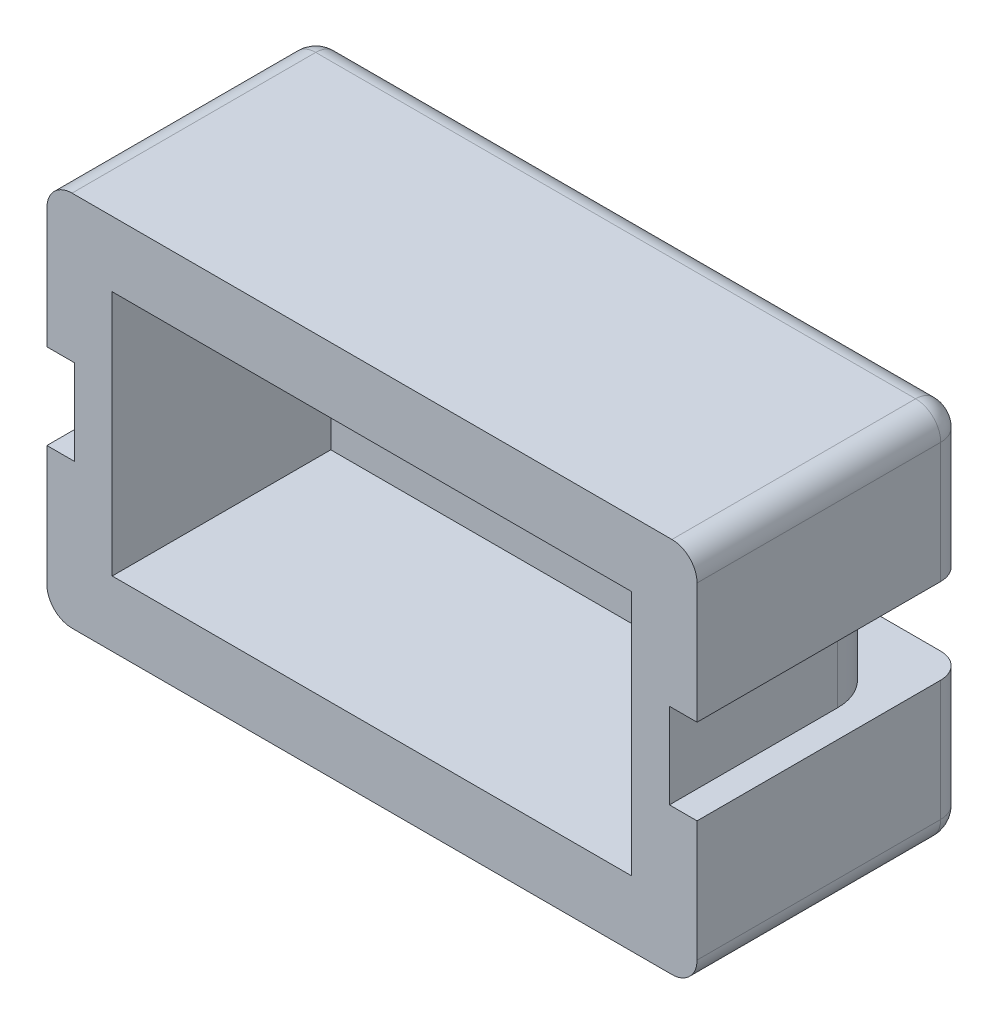
SolidWorks part; units mm, degrees
ref_plane "Front Plane" through (0, 0, 0) normal (0, 0, 1) x (1, 0, 0)
ref_plane "Top Plane" through (0, 0, 0) normal (0, 1, 0) x (1, 0, 0)
ref_plane "Right Plane" through (0, 0, 0) normal (1, 0, 0) x (0, 0, -1)
sketch "Sketch1" plane through (0, 0, 0) normal (0, 0, 1) x (1, 0, 0)
  line L0 (0, -2.7579) -> (0, 2.1887) construction
  line L9 (-3.3744, -0.8) -> (5.2209, -0.8) construction
  line L13 (-2.47, -1.6) -> (2.47, -1.6) construction
  line L14 (2.47, 0) -> (-2.47, 0) construction
  line L15 (-5.97, 0) -> (-5.97, -1.6) construction
  line L16 (6.47, -4.55) -> (-6.47, -4.55)
  line L17 (6.47, -4.55) -> (6.47, 2.95)
  line L18 (6.47, 2.95) -> (-6.47, 2.95)
  line L19 (-6.47, -4.55) -> (-6.47, 2.95)
  line L20 (6.47, -4.55) -> (-6.47, 2.95) construction
  line L21 (6.47, 2.95) -> (-6.47, -4.55) construction
  point P5 (0.9233, -0.8)
  point P12 (0, -0.8)
  dimension "D1" = 0.5
  dimension "D2" = 7.5
extrude "Boss-Extrude1" add sketch "Sketch1" against normal blind 5.35
fillet "Fillet1" radius 0.5 4 edges at (6.47, 2.95, -2.675) (-6.47, 2.95, -2.675) (-6.47, -4.55, -2.675) (6.47, -4.55, -2.675)
sketch "Sketch2" plane through (0, 0, 0) normal (0, 0, 1) x (1, 0, 0)
  line L8 (-5.17, 1.65) -> (-5.17, -3.25)
  line L9 (-5.17, -3.25) -> (5.17, -3.25)
  line L10 (5.17, -3.25) -> (5.17, 1.65)
  line L11 (5.17, 1.65) -> (-5.17, 1.65)
  line L12 (-5.17, 1.65) -> (-5.17, -3.25)
  line L13 (-5.17, -3.25) -> (5.17, -3.25)
  line L14 (5.17, -3.25) -> (5.17, 1.65)
  line L15 (5.17, 1.65) -> (-5.17, 1.65)
  dimension "D1" = 1.3
extrude "Cut-Extrude1" cut sketch "Sketch2" against normal offset from surface (4.35 mm away) 1 up to face at (0, -0.8, -5.35)
sketch "Sketch3" plane through (0, 0, -4.35) normal (0, 0, 1) x (1, 0, 0)
  line L0 (-5.17, -3.25) -> (-5.17, 1.65) construction
  line L1 (-5.17, -1.6) -> (5.17, -1.6)
  line L2 (-5.17, -1.6) -> (-5.17, 0)
  line L3 (-5.17, 0) -> (5.17, 0)
  line L4 (5.17, -1.6) -> (5.17, 0)
  line L5 (5.17, 1.65) -> (5.17, -3.25) construction
  line L6 (10, 0) -> (-10, 0) construction
  line L7 (-6.77, -1.6) -> (-10, -1.6) construction
extrude "Cut-Extrude2" cut sketch "Sketch3" against normal through all
sketch "Sketch4" plane through (0, -1.6, 0) normal (0, -1, 0) x (1, 0, 0)
  line L4 (5.97, -3.35) -> (5.97, -0.8) construction
  line L5 (4.27, -4.35) -> (4.97, -4.35) construction
  line L9 (-4.97, -4.35) -> (-4.27, -4.35) construction
  line L10 (-5.97, -3.35) -> (-5.97, -0.8) construction
  line L16 (5.97, -3.35) -> (5.97, 0)
  line L17 (4.27, -4.35) -> (4.97, -4.35)
  line L21 (-4.97, -4.35) -> (-4.27, -4.35)
  line L22 (-5.97, -3.35) -> (-5.97, 0)
  line L24 (4.27, -4.35) -> (-4.27, -4.35)
  line L25 (5.97, 0) -> (-5.97, 0)
  arc A5 (4.97, -4.35) -> (5.97, -3.35) centre (4.97, -3.35) ccw construction
  arc A10 (-5.97, -3.35) -> (-4.97, -4.35) centre (-4.97, -3.35) ccw construction
  arc A17 (4.97, -4.35) -> (5.97, -3.35) centre (4.97, -3.35) ccw
  arc A22 (-5.97, -3.35) -> (-4.97, -4.35) centre (-4.97, -3.35) ccw
extrude "Cut-Extrude3" cut sketch "Sketch4" against normal blind 1.6 flip side to cut
fillet "Fillet2" radius 0.5 10 edges at (6.47, 1.225, -5.35) (-6.47, 1.225, -5.35) (-6.3236, 2.8036, -5.35) (0, 2.95, -5.35) (6.3236, 2.8036, -5.35) (-6.47, -2.825, -5.35) (-6.3236, -4.4036, -5.35) (0, -4.55, -5.35) (6.47, -2.825, -5.35) (6.3236, -4.4036, -5.35)
sketch "Sketch5" plane through (0, 0, 0) normal (0, -1, 0) x (1, 0, 0)
  line L10 (-5.97, -5.35) -> (5.97, -5.35)
  line L11 (6.47, -4.85) -> (6.47, 0)
  line L12 (6.47, 0) -> (5.97, 0)
  line L13 (5.97, 0) -> (5.97, -3.35)
  line L14 (5.17, -4.3298) -> (5.17, -4.35)
  line L15 (5.17, -4.35) -> (-5.17, -4.35)
  line L16 (-5.17, -4.35) -> (-5.17, -4.3298)
  line L17 (-5.97, -3.35) -> (-5.97, 0)
  line L18 (-5.97, 0) -> (-6.47, 0)
  line L19 (-6.47, 0) -> (-6.47, -4.85)
  line L20 (-5.97, -5.35) -> (5.97, -5.35)
  line L21 (6.47, -4.85) -> (6.47, 0)
  line L22 (6.47, 0) -> (5.97, 0)
  line L23 (5.97, 0) -> (5.97, -3.35)
  line L24 (5.17, -4.3298) -> (5.17, -4.35)
  line L25 (5.17, -4.35) -> (-5.17, -4.35)
  line L26 (-5.17, -4.35) -> (-5.17, -4.3298)
  line L27 (-5.97, -3.35) -> (-5.97, 0)
  line L28 (-5.97, 0) -> (-6.47, 0)
  line L29 (-6.47, 0) -> (-6.47, -4.85)
  arc A4 (5.97, -5.35) -> (6.47, -4.85) centre (5.97, -4.85) ccw
  arc A5 (5.17, -4.3298) -> (5.97, -3.35) centre (4.97, -3.35) ccw
  arc A6 (-5.97, -3.35) -> (-5.17, -4.3298) centre (-4.97, -3.35) ccw
  arc A7 (-6.47, -4.85) -> (-5.97, -5.35) centre (-5.97, -4.85) ccw
  arc A8 (5.97, -5.35) -> (6.47, -4.85) centre (5.97, -4.85) ccw
  arc A9 (5.17, -4.3298) -> (5.97, -3.35) centre (4.97, -3.35) ccw
  arc A10 (-5.97, -3.35) -> (-5.17, -4.3298) centre (-4.97, -3.35) ccw
  arc A11 (-6.47, -4.85) -> (-5.97, -5.35) centre (-5.97, -4.85) ccw
  dimension "D1" = 0
extrude "Cut-Extrude4 - clearance for top" cut sketch "Sketch5" against normal blind 0.05
sketch "Sketch6" plane through (0, -1.6, 0) normal (0, 1, 0) x (1, 0, 0)
  line L10 (5.97, 5.35) -> (-5.97, 5.35)
  line L11 (-6.47, 4.85) -> (-6.47, 0)
  line L12 (-6.47, 0) -> (-5.97, 0)
  line L13 (-5.97, 0) -> (-5.97, 3.35)
  line L14 (-5.17, 4.3298) -> (-5.17, 4.35)
  line L15 (-5.17, 4.35) -> (5.17, 4.35)
  line L16 (5.17, 4.35) -> (5.17, 4.3298)
  line L17 (5.97, 3.35) -> (5.97, 0)
  line L18 (5.97, 0) -> (6.47, 0)
  line L19 (6.47, 0) -> (6.47, 4.85)
  line L20 (5.97, 5.35) -> (-5.97, 5.35)
  line L21 (-6.47, 4.85) -> (-6.47, 0)
  line L22 (-6.47, 0) -> (-5.97, 0)
  line L23 (-5.97, 0) -> (-5.97, 3.35)
  line L24 (-5.17, 4.3298) -> (-5.17, 4.35)
  line L25 (-5.17, 4.35) -> (5.17, 4.35)
  line L26 (5.17, 4.35) -> (5.17, 4.3298)
  line L27 (5.97, 3.35) -> (5.97, 0)
  line L28 (5.97, 0) -> (6.47, 0)
  line L29 (6.47, 0) -> (6.47, 4.85)
  arc A4 (-5.97, 5.35) -> (-6.47, 4.85) centre (-5.97, 4.85) ccw
  arc A5 (-5.17, 4.3298) -> (-5.97, 3.35) centre (-4.97, 3.35) ccw
  arc A6 (5.97, 3.35) -> (5.17, 4.3298) centre (4.97, 3.35) ccw
  arc A7 (6.47, 4.85) -> (5.97, 5.35) centre (5.97, 4.85) ccw
  arc A8 (-5.97, 5.35) -> (-6.47, 4.85) centre (-5.97, 4.85) ccw
  arc A9 (-5.17, 4.3298) -> (-5.97, 3.35) centre (-4.97, 3.35) ccw
  arc A10 (5.97, 3.35) -> (5.17, 4.3298) centre (4.97, 3.35) ccw
  arc A11 (6.47, 4.85) -> (5.97, 5.35) centre (5.97, 4.85) ccw
  dimension "D1" = 0
extrude "Cut-Extrude5 - clearance for bottom" cut sketch "Sketch6" against normal blind 0.05
sketch "Sketch7" plane through (0, 0.05, 0) normal (0, -1, 0) x (1, 0, 0)
  line L20 (-5.97, -5.4) -> (5.97, -5.4)
  line L21 (6.52, -4.85) -> (6.52, 0.05)
  line L22 (6.52, 0.05) -> (5.92, 0.05)
  line L23 (5.92, 0.05) -> (5.92, -3.35)
  line L24 (5.12, -4.2881) -> (5.12, -4.3)
  line L25 (5.12, -4.3) -> (-5.12, -4.3)
  line L26 (-5.12, -4.3) -> (-5.12, -4.2881)
  line L27 (-5.92, -3.35) -> (-5.92, 0.05)
  line L28 (-5.92, 0.05) -> (-6.52, 0.05)
  line L29 (-6.52, 0.05) -> (-6.52, -4.85)
  line L30 (-5.97, -5.4) -> (5.97, -5.4)
  line L31 (6.52, -4.85) -> (6.52, 0.05)
  line L32 (6.52, 0.05) -> (5.92, 0.05)
  line L33 (5.92, 0.05) -> (5.92, -3.35)
  line L34 (5.12, -4.2881) -> (5.12, -4.3)
  line L35 (5.12, -4.3) -> (-5.12, -4.3)
  line L36 (-5.12, -4.3) -> (-5.12, -4.2881)
  line L37 (-5.92, -3.35) -> (-5.92, 0.05)
  line L38 (-5.92, 0.05) -> (-6.52, 0.05)
  line L39 (-6.52, 0.05) -> (-6.52, -4.85)
  arc A8 (-6.52, -4.85) -> (-5.97, -5.4) centre (-5.97, -4.85) ccw
  arc A9 (5.97, -5.4) -> (6.52, -4.85) centre (5.97, -4.85) ccw
  arc A10 (5.12, -4.2881) -> (5.92, -3.35) centre (4.97, -3.35) ccw
  arc A11 (-5.92, -3.35) -> (-5.12, -4.2881) centre (-4.97, -3.35) ccw
  arc A12 (-6.52, -4.85) -> (-5.97, -5.4) centre (-5.97, -4.85) ccw
  arc A13 (5.97, -5.4) -> (6.52, -4.85) centre (5.97, -4.85) ccw
  arc A14 (5.12, -4.2881) -> (5.92, -3.35) centre (4.97, -3.35) ccw
  arc A15 (-5.92, -3.35) -> (-5.12, -4.2881) centre (-4.97, -3.35) ccw
  dimension "D1" = 0.05
extrude "Cut-Extrude6 - clearance on sides" cut sketch "Sketch7" along normal up to surface (1.7 mm away) up to face at (0, -1.65, -3.2108)
